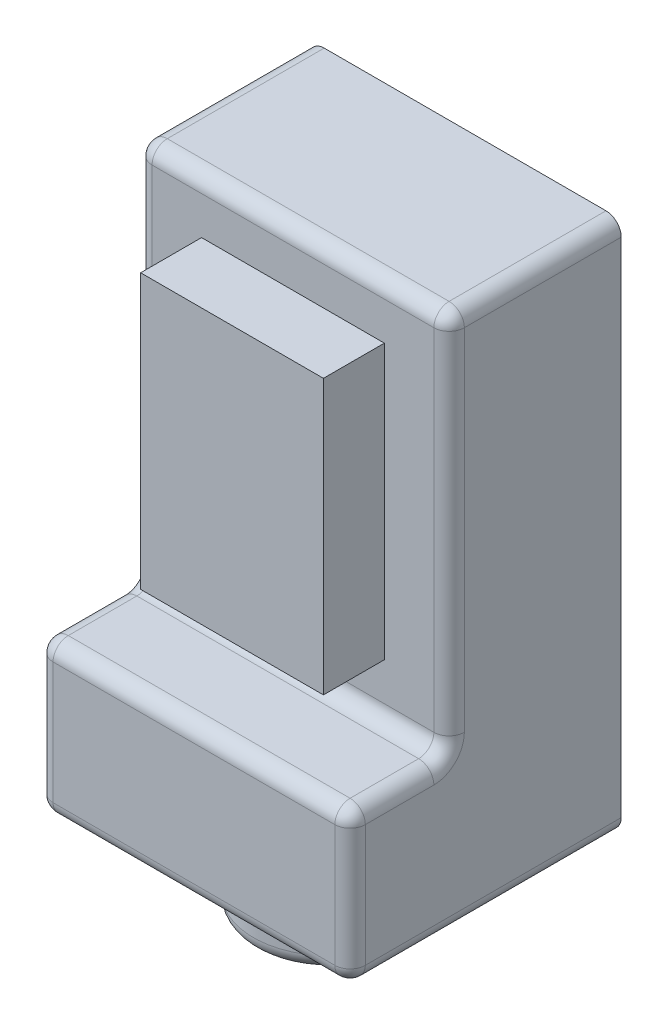
SolidWorks part; units mm, degrees
ref_plane "前基準面" through (0, 0, 0) normal (0, 0, 1) x (1, 0, 0)
ref_plane "上基準面" through (0, 0, 0) normal (0, 1, 0) x (1, 0, 0)
ref_plane "右基準面" through (0, 0, 0) normal (1, 0, 0) x (0, 0, -1)
sketch "草圖1" plane through (0, 0, 0) normal (0, 0, 1) x (1, 0, 0)
  line L1 (-10.25, -17.5) -> (10.25, -17.5)
  line L2 (-10.25, -17.5) -> (-10.25, 17.5)
  line L3 (-10.25, 17.5) -> (10.25, 17.5)
  line L4 (10.25, -17.5) -> (10.25, 17.5)
  line L5 (-10.25, -17.5) -> (10.25, 17.5) construction
  line L6 (-10.25, 17.5) -> (10.25, -17.5) construction
  point P0 (0, 0)
  dimension "D1" = 35
  dimension "D2" = 20.5
extrude "填料-伸長1" add sketch "草圖1" along normal blind 17.8
sketch "草圖3" plane through (0, -17.5, 0) normal (0, -1, 0) x (1, 0, 0)
  line L0 (0, 17.8) -> (0, 0) construction
  line L1 (-10.25, 17.8) -> (10.25, 17.8) construction
  line L2 (-10.25, 0) -> (10.25, 0) construction
  circle A0 centre (0, 8.9) radius 3
  dimension "D1" = 6
extrude "填料-伸長2" add sketch "草圖3" along normal blind 2
sketch "草圖4" plane through (0, -19.5, 0) normal (0, -1, 0) x (1, 0, 0)
  circle A0 centre (0, 8.9) radius 5
  dimension "D1" = 10
extrude "填料-伸長3" add sketch "草圖4" along normal blind 3
sketch "草圖5" plane through (0, 0, 17.8) normal (0, 0, 1) x (1, 0, 0)
  line L0 (10.25, -17.5) -> (10.25, 17.5) construction
  line L1 (-10.25, 17.5) -> (10.25, 17.5)
  line L2 (-10.25, 17.5) -> (-10.25, -7.5)
  line L3 (-10.25, -7.5) -> (10.25, -7.5)
  line L4 (10.25, 17.5) -> (10.25, -7.5)
  dimension "D1" = 25
extrude "除料-伸長1" cut sketch "草圖5" against normal blind 6.5
fillet "圓角1" radius 1 15 edges at (0, -17.5, 17.8) (-10.25, -12.5, 17.8) (10.25, -12.5, 17.8) (-10.25, -7.5, 14.55) (10.25, -7.5, 14.55) (0, -7.5, 17.8) (0, 17.5, 11.3) (10.25, 5, 11.3) (0, -7.5, 11.3) (-10.25, 5, 11.3) (10.25, -17.5, 8.9) (-10.25, -17.5, 8.9) (-10.25, 17.5, 5.65) (10.25, 17.5, 5.65) (0, -22.5, 3.9)
sketch "草圖6" plane through (0, 0, 11.3) normal (0, 0, 1) x (1, 0, 0)
  line L0 (0, -6.5) -> (0, 16.5) construction
  line L1 (6, -4) -> (-6, -4)
  line L2 (6, -4) -> (6, 14)
  line L3 (6, 14) -> (-6, 14)
  line L4 (-6, -4) -> (-6, 14)
  line L5 (6, -4) -> (-6, 14) construction
  line L6 (6, 14) -> (-6, -4) construction
  line L7 (-9.25, -6.5) -> (9.25, -6.5) construction
  line L8 (9.25, 16.5) -> (-9.25, 16.5) construction
  line L9 (-9.25, 5) -> (9.25, 5) construction
  line L10 (-9.25, 16.5) -> (-9.25, -6.5) construction
  line L11 (9.25, -6.5) -> (9.25, 16.5) construction
  point P0 (0, 5)
  dimension "D1" = 18
  dimension "D2" = 12
extrude "填料-伸長4" add sketch "草圖6" along normal blind 4
